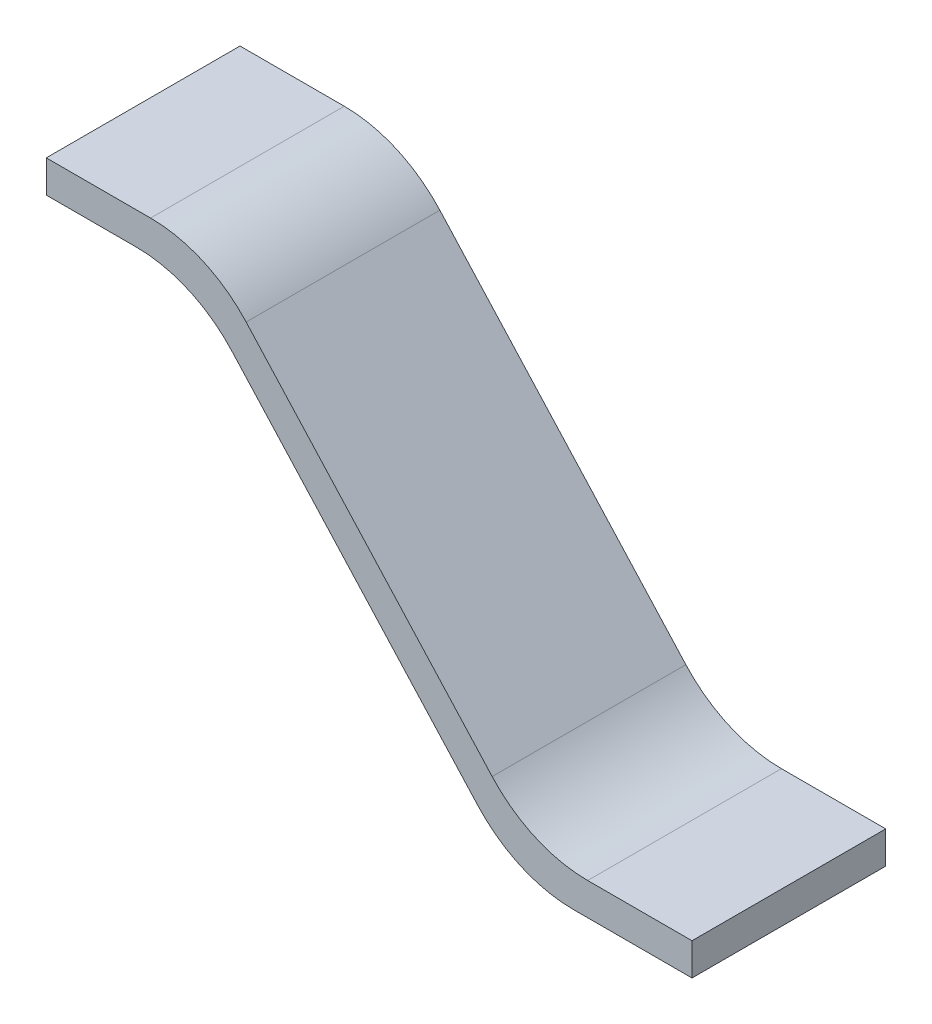
SolidWorks part; units mm, degrees
ref_plane "Front Plane" through (0, 0, 0) normal (0, 0, 1) x (1, 0, 0)
ref_plane "Top Plane" through (0, 0, 0) normal (0, 1, 0) x (1, 0, 0)
ref_plane "Right Plane" through (0, 0, 0) normal (1, 0, 0) x (0, 0, -1)
sketch "Sketch4" plane through (0, 0, 0) normal (0, 0, 1) x (1, 0, 0)
  line L0 (0, 0) -> (0.25, 0)
  line L1 (0.25, 0) -> (0.75, -0.55)
  line L2 (0.75, -0.55) -> (1, -0.55)
  line L3 (0, -0.05) -> (0.2279, -0.05)
  line L4 (0.2279, -0.05) -> (0.7279, -0.6)
  line L5 (0.7279, -0.6) -> (1, -0.6)
  line L6 (0, -0.05) -> (0, 0)
  line L7 (1, -0.6) -> (1, -0.55)
  dimension "D1" = 0.6
  dimension "D2" = 0.25
  dimension "D3" = 0.25
  dimension "D4" = 0.5
  dimension "D5" = 0.05
extrude "Boss-Extrude1" add sketch "Sketch4" along normal mid plane 0.3
fillet "Fillet4" radius 0.2 4 edges at (0.2279, -0.05, 0) (0.7279, -0.6, 0) (0.75, -0.55, 0) (0.25, 0, 0)
